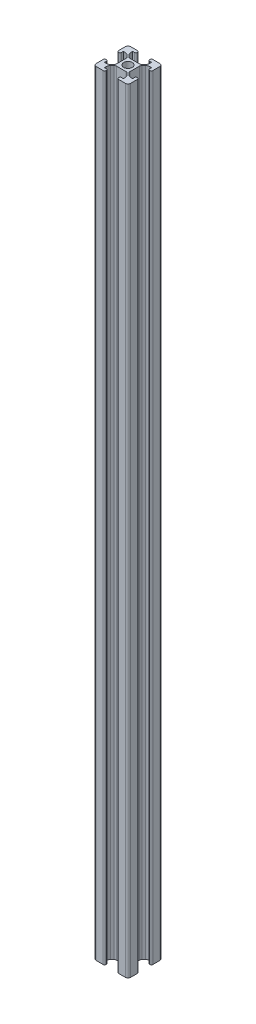
SolidWorks part; units mm, degrees
ref_plane "Front" through (0, 0, 0) normal (0, 0, 1) x (1, 0, 0)
ref_plane "Top" through (0, 0, 0) normal (0, 1, 0) x (1, 0, 0)
ref_plane "Right" through (0, 0, 0) normal (1, 0, 0) x (0, 0, -1)
sketch "Sketch2" plane through (0, 0, 0) normal (0, 1, 0) x (1, 0, 0)
  line L0 (-5.4, 4.8697) -> (-4.3393, 3.809)
  line L1 (-8.5, 10) -> (-4.4, 10)
  line L3 (-8.5, -10) -> (-4.4, -10)
  line L4 (10, 8.5) -> (10, 4.4)
  line L5 (-10, 10) -> (-9.5607, 9.5607) construction
  line L6 (-10, -10) -> (-9.5607, -9.5607) construction
  line L7 (-2.7483, 3.9) -> (2.7483, 3.9)
  line L8 (-3.9, 2.7483) -> (-3.9, -2.7483)
  line L9 (-2.7483, -3.9) -> (2.7483, -3.9)
  line L10 (3.9, 2.7483) -> (3.9, -2.7483)
  line L11 (-5.5, -8.2) -> (-4.4, -8.2)
  line L12 (-3.6, -9.2) -> (-3.6, -9)
  line L13 (-4.8697, 5.4) -> (-3.809, 4.3393)
  line L14 (4.8697, 5.4) -> (3.809, 4.3393)
  line L15 (5.4, 4.8697) -> (4.3393, 3.809)
  line L16 (-5.5, -8.2) -> (-5.5, -7.2)
  line L17 (9.5607, -9.5607) -> (10, -10) construction
  line L18 (-3.809, -4.3393) -> (-4.8697, -5.4)
  line L19 (-4.3393, -3.809) -> (-5.4, -4.8697)
  line L20 (3.809, -4.3393) -> (4.8697, -5.4)
  line L21 (4.3393, -3.809) -> (5.4, -4.8697)
  line L22 (9.5607, 9.5607) -> (10, 10) construction
  line L23 (8.5, -10) -> (4.4, -10)
  line L24 (3.6, -9.2) -> (3.6, -9)
  line L25 (5.5, -8.2) -> (4.4, -8.2)
  line L26 (0, 7.192) -> (0, -12.1556) construction
  line L27 (5.5, -8.2) -> (5.5, -7.2)
  line L28 (-8.2, 5.5) -> (-7.2, 5.5)
  line L29 (-8.2, 5.5) -> (-8.2, 4.4)
  line L30 (-10, 8.5) -> (-10, 4.4)
  line L31 (-8.2, -5.5) -> (-7.2, -5.5)
  line L32 (-10, -8.5) -> (-10, -4.4)
  line L33 (-8.2, -5.5) -> (-8.2, -4.4)
  line L34 (5.5, 8.2) -> (5.5, 7.2)
  line L35 (5.5, 8.2) -> (4.4, 8.2)
  line L36 (8.5, 10) -> (4.4, 10)
  line L37 (-5.5, 8.2) -> (-5.5, 7.2)
  line L38 (3.6, 9.2) -> (3.6, 9)
  line L39 (-5.5, 8.2) -> (-4.4, 8.2)
  line L40 (8.2, -5.5) -> (7.2, -5.5)
  line L41 (8.2, -5.5) -> (8.2, -4.4)
  line L42 (-3.6, 9.2) -> (-3.6, 9)
  line L43 (8.2, 5.5) -> (7.2, 5.5)
  line L44 (10, -4.4) -> (10, -8.5)
  line L45 (8.2, 5.5) -> (8.2, 4.4)
  line L46 (9, -3.6) -> (9.2, -3.6)
  line L47 (9, 3.6) -> (9.2, 3.6)
  line L48 (-9.2, 3.6) -> (-9, 3.6)
  line L49 (-9.2, -3.6) -> (-9, -3.6)
  line L52 (-8.5, 10) -> (-4.4, 10) [skipped]
  line L53 (10, -8.5) -> (10, -4.4) [skipped]
  line L54 (10, 8.5) -> (10, 4.4) [skipped]
  arc A0 (-10, -8.5) -> (-8.5, -10) centre (-8.5, -8.5) ccw
  arc A1 (8.5, -10) -> (10, -8.5) centre (8.5, -8.5) ccw
  arc A2 (8.5, 10) -> (10, 8.5) centre (8.5, 8.5) cw
  arc A3 (-8.5, 10) -> (-10, 8.5) centre (-8.5, 8.5) ccw
  arc A4 (-3.9, -2.7483) -> (-4.3393, -3.809) centre (-5.4, -2.7483) cw
  arc A5 (-2.7483, -3.9) -> (-3.809, -4.3393) centre (-2.7483, -5.4) ccw
  arc A6 (2.7483, -3.9) -> (3.809, -4.3393) centre (2.7483, -5.4) cw
  arc A7 (3.9, -2.7483) -> (4.3393, -3.809) centre (5.4, -2.7483) ccw
  arc A8 (3.9, 2.7483) -> (4.3393, 3.809) centre (5.4, 2.7483) cw
  arc A9 (2.7483, 3.9) -> (3.809, 4.3393) centre (2.7483, 5.4) ccw
  arc A10 (-2.7483, 3.9) -> (-3.809, 4.3393) centre (-2.7483, 5.4) cw
  arc A11 (-3.9, 2.7483) -> (-4.3393, 3.809) centre (-5.4, 2.7483) ccw
  arc A12 (-5.5, -7.2) -> (-4.8697, -5.4) centre (-2.6148, -7.2) cw
  arc A13 (-3.6, -9.2) -> (-4.4, -10) centre (-4.4, -9.2) cw
  arc A14 (-3.6, -9) -> (-4.4, -8.2) centre (-4.4, -9) ccw
  arc A15 (3.6, -9.2) -> (4.4, -10) centre (4.4, -9.2) ccw
  arc A16 (3.6, -9) -> (4.4, -8.2) centre (4.4, -9) cw
  arc A17 (5.5, -7.2) -> (4.8697, -5.4) centre (2.6148, -7.2) ccw
  arc A18 (-7.2, 5.5) -> (-5.4, 4.8697) centre (-7.2, 2.6148) cw
  arc A19 (-9, 3.6) -> (-8.2, 4.4) centre (-9, 4.4) ccw
  arc A20 (-9.2, 3.6) -> (-10, 4.4) centre (-9.2, 4.4) cw
  arc A21 (-7.2, -5.5) -> (-5.4, -4.8697) centre (-7.2, -2.6148) ccw
  arc A22 (-9, -3.6) -> (-8.2, -4.4) centre (-9, -4.4) cw
  arc A23 (-9.2, -3.6) -> (-10, -4.4) centre (-9.2, -4.4) ccw
  arc A24 (5.5, 7.2) -> (4.8697, 5.4) centre (2.6148, 7.2) cw
  arc A25 (3.6, 9) -> (4.4, 8.2) centre (4.4, 9) ccw
  arc A26 (3.6, 9.2) -> (4.4, 10) centre (4.4, 9.2) cw
  arc A27 (-5.5, 7.2) -> (-4.8697, 5.4) centre (-2.6148, 7.2) ccw
  arc A28 (-3.6, 9) -> (-4.4, 8.2) centre (-4.4, 9) cw
  arc A29 (-3.6, 9.2) -> (-4.4, 10) centre (-4.4, 9.2) ccw
  arc A30 (7.2, -5.5) -> (5.4, -4.8697) centre (7.2, -2.6148) cw
  arc A31 (9, -3.6) -> (8.2, -4.4) centre (9, -4.4) ccw
  arc A32 (9.2, -3.6) -> (10, -4.4) centre (9.2, -4.4) cw
  arc A33 (7.2, 5.5) -> (5.4, 4.8697) centre (7.2, 2.6148) ccw
  arc A34 (9, 3.6) -> (8.2, 4.4) centre (9, 4.4) cw
  arc A35 (9.2, 3.6) -> (10, 4.4) centre (9.2, 4.4) ccw
  circle A36 centre (0, 0) radius 2.5
  point P0 (0, 0)
  point P6 (0, 0)
  point P41 (-3.9, -3.3697)
  point P44 (-3.3697, -3.9)
  point P47 (3.3697, -3.9)
  point P50 (3.9, -3.3697)
  dimension "D5" = 1.5
  dimension "D3" = 1.5
  dimension "D9" = 0.8
  dimension "D1" = 20
  dimension "D2" = 20
  dimension "D4" = 4
  dimension "D6" = 0.75
  dimension "D8" = 1.8
  dimension "D10" = 1
  dimension "D7" = 2
extrude "Boss-Extrude1" add sketch "Sketch2" along normal blind 450
